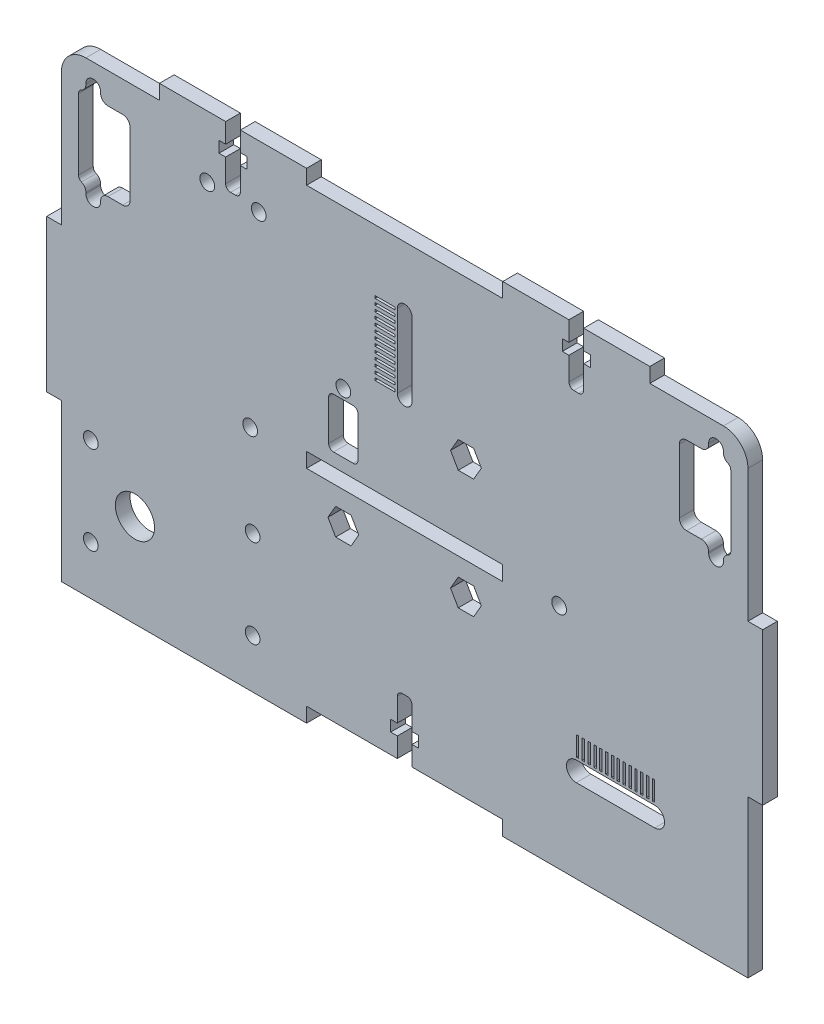
SolidWorks part; units mm, degrees
other "Marcação1"
sketch "Esboço7" plane through (-68, 31.5, 3) normal (-0.6758, 0.2828, 0.6807) x (0.7271, 0.1043, 0.6785)
sketch "Esboço8" plane through (-68, 31.5, 3) normal (-0.6758, 0.2828, 0.6807) x (0.7271, 0.1043, 0.6785)
sketch "Esboço9" plane through (-68, 31.5, 3) normal (-0.6758, 0.2828, 0.6807) x (0.7271, 0.1043, 0.6785)
sketch "Esboço10" plane through (-68, 31.5, 3) normal (-0.6758, 0.2828, 0.6807) x (0.7271, 0.1043, 0.6785)
sketch "Esboço11" plane through (-68, 36.25, 3) normal (-0.6758, 0.2828, 0.6807) x (0.7271, 0.1043, 0.6785)
sketch "Esboço13" plane through (-68, 36.25, 3) normal (-0.6758, 0.2828, 0.6807) x (0.7271, 0.1043, 0.6785)
sketch "Esboço15" plane through (-68, 36.25, 3) normal (-0.6758, 0.2828, 0.6807) x (0.7271, 0.1043, 0.6785)
sketch "Esboço19" plane through (-68, 66.25, 3) normal (-0.6758, 0.2828, 0.6807) x (0.7271, 0.1043, 0.6785)
sketch "Esboço22" plane through (-68, 95.5577, 3) normal (-0.6758, 0.2828, 0.6807) x (0.7271, 0.1043, 0.6785)
material "Acrylic (Medium-high impact)"
ref_plane "Plano frontal" through (0, 0, 0) normal (0, 0, 1) x (1, 0, 0)
ref_plane "Plano superior" through (0, 0, 0) normal (0, 1, 0) x (1, 0, 0)
ref_plane "Plano direito" through (0, 0, 0) normal (1, 0, 0) x (0, 0, -1)
sketch "Esboço1" plane through (0, 0, 0) normal (0, 0, 1) x (1, 0, 0)
  line L6 (70, -47.5) -> (-70, -47.5)
  line L8 (70, -47.5) -> (70, 47.5)
  line L9 (70, 47.5) -> (-70, 47.5)
  line L10 (-70, -47.5) -> (-70, 47.5)
  line L11 (70, -47.5) -> (-70, 47.5) construction
  line L12 (70, 47.5) -> (-70, -47.5) construction
  point P0 (0, 0)
  dimension "D1" = 95
  dimension "D2" = 140
extrude "Ressalto-extrusão1" add sketch "Esboço1" along normal mid plane 3
sketch "Esboço2" plane through (0, 0, 1.5) normal (0, 0, 1) x (1, 0, 0)
  line L1 (-20, -47.5) -> (20, -47.5)
  line L2 (-20, -47.5) -> (-20, -44.5)
  line L3 (-20, -44.5) -> (20, -44.5)
  line L4 (20, -47.5) -> (20, -44.5)
  line L6 (-70, -47.5) -> (70, -47.5) construction
  line L21 (-20, 0.5) -> (20, 0.5)
  line L22 (-20, 0.5) -> (-20, -2.5)
  line L23 (-20, -2.5) -> (20, -2.5)
  line L24 (20, 0.5) -> (20, -2.5)
  line L25 (-20, 0.5) -> (20, -2.5) construction
  line L26 (-20, -2.5) -> (20, 0.5) construction
  line L28 (0, -1.65) -> (0, 1.65) construction
  circle A2 centre (-31.5, -1) radius 1.5
  circle A4 centre (31.5, -1) radius 1.5
  point P6 (0, -44.5)
  point P14 (0, -1)
  point P29 (-20, -1)
  dimension "D4" = 11.5
  dimension "D8" = 3
  dimension "D3" = 3
  dimension "D2" = 40
  dimension "D5" = 45
  dimension "D6" = 3
  dimension "D13" = 40
extrude "Corte-extrusão1" cut sketch "Esboço2" against normal through all
sketch "Sketch9" plane through (0, 0, 0) normal (0, 0, 1) x (1, 0, 0)
  line L0 (20, -44.5) -> (-20, -44.5) construction
  line L1 (-1.5, -44.5) -> (1.5, -44.5)
  line L2 (-1.5, -44.5) -> (-1.5, -40.5)
  line L3 (-0.5, -32.5) -> (0.5, -32.5)
  line L4 (1.5, -44.5) -> (1.5, -40.5)
  line L5 (1.5, -38.23) -> (2.85, -38.23)
  line L6 (-2.85, -38.23) -> (-1.5, -38.23)
  line L7 (-2.85, -38.23) -> (-2.85, -40.5)
  line L8 (-2.85, -40.5) -> (-1.5, -40.5)
  line L9 (2.85, -38.23) -> (2.85, -40.5)
  line L10 (-1.5, -38.23) -> (-1.5, -33.5)
  line L11 (1.5, -40.5) -> (2.85, -40.5)
  line L12 (1.5, -38.23) -> (1.5, -33.5)
  arc A0 (0.5, -32.5) -> (1.5, -33.5) centre (0.5, -33.5) cw
  arc A1 (-1.5, -33.5) -> (-0.5, -32.5) centre (-0.5, -33.5) cw
  point P6 (0, -32.5)
  point P18 (1.5, -32.5)
  point P21 (-1.5, -32.5)
  dimension "D7" = 1
  dimension "D1" = 3
  dimension "D2" = 12
  dimension "D3" = 2.27
  dimension "D4" = 1.35
  dimension "D5" = 1.35
  dimension "D6" = 4
extrude "Cut-Extrude12" cut sketch "Sketch9" against normal through all both and the other way through all
sketch "Esboço3" plane through (0, 0, 1.5) normal (0, 0, 1) x (1, 0, 0)
  line L0 (70, -47.5) -> (70, 47.5) construction
  line L1 (70, 15.5) -> (73, 15.5)
  line L2 (70, 15.5) -> (70, -15.5)
  line L3 (70, -15.5) -> (73, -15.5)
  line L4 (73, 15.5) -> (73, -15.5)
  line L5 (0, -1.65) -> (0, 1.65) construction
  line L6 (-70, -15.5) -> (-73, -15.5)
  line L7 (-70, 15.5) -> (-73, 15.5)
  line L8 (-70, 15.5) -> (-70, -15.5)
  line L9 (-73, 15.5) -> (-73, -15.5)
  line L15 (70, 47.5) -> (-70, 47.5) construction
  line L16 (-50, 47.5) -> (-20, 47.5)
  line L17 (-50, 47.5) -> (-50, 50.5)
  line L18 (-50, 50.5) -> (-20, 50.5)
  line L19 (-20, 47.5) -> (-20, 50.5)
  line L20 (20, 47.5) -> (20, 50.5)
  line L21 (50, 50.5) -> (20, 50.5)
  line L22 (50, 47.5) -> (50, 50.5)
  line L23 (50, 47.5) -> (20, 47.5)
  line L24 (-70, 47.5) -> (-70, -47.5) construction
  point P6 (70, 0)
  dimension "D1" = 3
  dimension "D2" = 31
  dimension "D3" = 30
  dimension "D4" = 20
  dimension "D5" = 20
extrude "Ressalto-extrusão2" add sketch "Esboço3" against normal through all
sketch "Esboço30" plane through (0, 0, -1.5) normal (0, 0, -1) x (-1, 0, 0)
  line L0 (73, 15.5) -> (73, -15.5) construction
  line L6 (70, -47.5) -> (20, -47.5) construction
  circle A1 centre (55, -28.5) radius 4
  dimension "D1" = 18
  dimension "D2" = 19
  dimension "D3" = 8
extrude "Corte-extrusão11" cut sketch "Esboço30" against normal through all both and the other way through all
sketch "Esboço4" plane through (0, 0, 1.5) normal (0, 0, 1) x (1, 0, 0)
  line L0 (35, -28.5) -> (51, -28.5) construction
  line L1 (35, -26.5) -> (51, -26.5)
  line L2 (35, -30.5) -> (51, -30.5)
  line L4 (35, -26) -> (35.5, -26)
  line L5 (35, -26) -> (35, -22)
  line L6 (35, -22) -> (35.5, -22)
  line L7 (35.5, -26) -> (35.5, -22)
  line L8 (36.1923, -26) -> (36.6923, -26)
  line L9 (36.1923, -26) -> (36.1923, -22)
  line L10 (36.1923, -22) -> (36.6923, -22)
  line L11 (36.6923, -26) -> (36.6923, -22)
  line L12 (37.3846, -26) -> (37.8846, -26)
  line L13 (37.3846, -26) -> (37.3846, -22)
  line L14 (37.3846, -22) -> (37.8846, -22)
  line L15 (37.8846, -26) -> (37.8846, -22)
  line L16 (38.5769, -26) -> (39.0769, -26)
  line L17 (38.5769, -26) -> (38.5769, -22)
  line L18 (38.5769, -22) -> (39.0769, -22)
  line L19 (39.0769, -26) -> (39.0769, -22)
  line L20 (39.7692, -26) -> (40.2692, -26)
  line L21 (39.7692, -26) -> (39.7692, -22)
  line L22 (39.7692, -22) -> (40.2692, -22)
  line L23 (40.2692, -26) -> (40.2692, -22)
  line L24 (40.9615, -26) -> (41.4615, -26)
  line L25 (40.9615, -26) -> (40.9615, -22)
  line L26 (40.9615, -22) -> (41.4615, -22)
  line L27 (41.4615, -26) -> (41.4615, -22)
  line L28 (42.1538, -26) -> (42.6538, -26)
  line L29 (42.1538, -26) -> (42.1538, -22)
  line L30 (42.1538, -22) -> (42.6538, -22)
  line L31 (42.6538, -26) -> (42.6538, -22)
  line L32 (43.3462, -26) -> (43.8462, -26)
  line L33 (43.3462, -26) -> (43.3462, -22)
  line L34 (43.3462, -22) -> (43.8462, -22)
  line L35 (43.8462, -26) -> (43.8462, -22)
  line L36 (44.5385, -26) -> (45.0385, -26)
  line L37 (44.5385, -26) -> (44.5385, -22)
  line L38 (44.5385, -22) -> (45.0385, -22)
  line L39 (45.0385, -26) -> (45.0385, -22)
  line L40 (45.7308, -26) -> (46.2308, -26)
  line L41 (45.7308, -26) -> (45.7308, -22)
  line L42 (45.7308, -22) -> (46.2308, -22)
  line L43 (46.2308, -26) -> (46.2308, -22)
  line L44 (46.9231, -26) -> (47.4231, -26)
  line L45 (46.9231, -26) -> (46.9231, -22)
  line L46 (46.9231, -22) -> (47.4231, -22)
  line L47 (47.4231, -26) -> (47.4231, -22)
  line L48 (48.1154, -26) -> (48.6154, -26)
  line L49 (48.1154, -26) -> (48.1154, -22)
  line L50 (48.1154, -22) -> (48.6154, -22)
  line L51 (48.6154, -26) -> (48.6154, -22)
  line L52 (49.3077, -26) -> (49.8077, -26)
  line L53 (49.3077, -26) -> (49.3077, -22)
  line L54 (49.3077, -22) -> (49.8077, -22)
  line L55 (49.8077, -26) -> (49.8077, -22)
  line L56 (50.5, -26) -> (51, -26)
  line L57 (50.5, -26) -> (50.5, -22)
  line L58 (50.5, -22) -> (51, -22)
  line L59 (51, -26) -> (51, -22)
  line L60 (20, -47.5) -> (70, -47.5) construction
  arc A9 (35, -26.5) -> (35, -30.5) centre (35, -28.5) ccw
  circle A10 centre (43, -28.5) radius 2 construction
  arc A12 (51, -30.5) -> (51, -26.5) centre (51, -28.5) ccw
  circle A13 centre (-55, -28.5) radius 4 construction
  point P8 (43, -28.5)
  dimension "D1" = 98
  dimension "D4" = 0.5
  dimension "D3" = 8
  dimension "D2" = 4
  dimension "D5" = 4
  dimension "D6" = 14
  dimension "D7" = 0.5
  dimension "D8" = 19
extrude "Corte-extrusão2" cut sketch "Esboço4" against normal through all
sketch "Esboço31" plane through (0, 0, -1.5) normal (0, 0, -1) x (-1, 0, 0)
  line L0 (73, -15.5) -> (70, -15.5) construction
  line L1 (70, -15.5) -> (70, -47.5) construction
  circle A4 centre (64, -19.5) radius 1.5
  circle A5 centre (64, -37.5) radius 1.5
  circle A7 centre (31, -19.5) radius 1.5
  circle A8 centre (31, -37.5) radius 1.5
  dimension "D1" = 3
  dimension "D2" = 4
  dimension "D3" = 6
  dimension "D4" = 18
  dimension "D5" = 33
extrude "Corte-extrusão12" cut sketch "Esboço31" against normal through all both and the other way through all
sketch "Sketch8" plane through (0, 0, -1.5) normal (0, 0, -1) x (-1, 0, 0)
  line L2 (-70, 47.5) -> (-50, 47.5) construction
  line L4 (0, 1.65) -> (0, -1.65) construction
  line L5 (-70, 15.5) -> (-70, 47.5) construction
  line B0 (-70, 33.25) -> (-56, 33.25) construction
  line B1 (-70, 39.75) -> (-70, 26.75) construction
  line B2 (-56, 39.75) -> (-56, 26.75)
  line B3 (-65, 23.5) -> (-65, 23.75)
  line B4 (-62, 23.5) -> (-62, 23.75)
  line B5 (-60.5, 25.25) -> (-57.5, 25.25)
  line B6 (-65, 43) -> (-65, 42.75)
  line B7 (-62, 43) -> (-62, 42.75)
  line B8 (-60.5, 41.25) -> (-57.5, 41.25)
  line B9 (-66.5, 40.4587) -> (-66.5, 26.0413)
  arc B10 (-62, 43) -> (-65, 43) centre (-63.5, 43) ccw
  arc B11 (-65, 23.5) -> (-62, 23.5) centre (-63.5, 23.5) ccw
  arc B12 (-62, 23.75) -> (-60.5, 25.25) centre (-60.5, 23.75) cw
  arc B13 (-65, 23.75) -> (-65.9, 25.1248) centre (-66.5, 23.75) ccw
  arc B14 (-62, 42.75) -> (-60.5, 41.25) centre (-60.5, 42.75) ccw
  arc B15 (-65, 42.75) -> (-65.9, 41.3752) centre (-66.5, 42.75) cw
  arc B16 (-57.5, 25.25) -> (-56, 26.75) centre (-57.5, 26.75) ccw
  arc B17 (-57.5, 41.25) -> (-56, 39.75) centre (-57.5, 39.75) cw
  arc B18 (-66.5, 26.0413) -> (-65.9, 25.1248) centre (-65.5, 26.0413) ccw
  arc B19 (-66.5, 40.4587) -> (-65.9, 41.3752) centre (-65.5, 40.4587) cw
  line B20 (70, 33.25) -> (56, 33.25) construction
  line B21 (56, 39.75) -> (56, 26.75)
  line B22 (65, 23.5) -> (65, 23.75)
  line B23 (62, 23.5) -> (62, 23.75)
  line B24 (60.5, 25.25) -> (57.5, 25.25)
  line B25 (65, 43) -> (65, 42.75)
  line B26 (62, 43) -> (62, 42.75)
  line B27 (60.5, 41.25) -> (57.5, 41.25)
  line B28 (66.5, 40.4587) -> (66.5, 26.0413)
  arc B29 (62, 43) -> (65, 43) centre (63.5, 43) cw
  arc B30 (65, 23.5) -> (62, 23.5) centre (63.5, 23.5) cw
  arc B31 (62, 23.75) -> (60.5, 25.25) centre (60.5, 23.75) ccw
  arc B32 (65, 23.75) -> (65.9, 25.1248) centre (66.5, 23.75) cw
  arc B33 (62, 42.75) -> (60.5, 41.25) centre (60.5, 42.75) cw
  arc B34 (65, 42.75) -> (65.9, 41.3752) centre (66.5, 42.75) ccw
  arc B35 (57.5, 25.25) -> (56, 26.75) centre (57.5, 26.75) cw
  arc B36 (57.5, 41.25) -> (56, 39.75) centre (57.5, 39.75) ccw
  arc B37 (66.5, 26.0413) -> (65.9, 25.1248) centre (65.5, 26.0413) cw
  arc B38 (66.5, 40.4587) -> (65.9, 41.3752) centre (65.5, 40.4587) ccw
  dimension "D3" = 3
sketch_block_instance "Block6-1"
sketch_block "Block6" parameters "D1"=3, "D2"=1.5, "D3"=1.5, "D5"=1, "D4"=5, "D6"=6.5
sketch_block_instance "Block6-4"
extrude "Cut-Extrude11" cut sketch "Sketch8" against normal through all both and the other way through all
sketch "Sketch11" plane through (0, 0, 0) normal (0, 0, 1) x (1, 0, 0)
  line L0 (50, 50.5) -> (20, 50.5) construction
  line L1 (33.5, 50.5) -> (36.5, 50.5)
  line L2 (33.5, 50.5) -> (33.5, 46.5)
  line L3 (34.5, 38.5) -> (35.5, 38.5)
  line L4 (36.5, 50.5) -> (36.5, 46.5)
  line L5 (20, 50.5) -> (20, 47.5) construction
  line L6 (33.5, 44.23) -> (33.5, 39.5)
  line L7 (32.15, 46.5) -> (33.5, 46.5)
  line L8 (32.15, 46.5) -> (32.15, 44.23)
  line L9 (32.15, 44.23) -> (33.5, 44.23)
  line L10 (37.85, 46.5) -> (37.85, 44.23)
  line L11 (36.5, 46.5) -> (37.85, 46.5)
  line L12 (36.5, 44.23) -> (36.5, 39.5)
  line L13 (36.5, 44.23) -> (37.85, 44.23)
  line L14 (0, -1.65) -> (0, 1.65) construction
  line L15 (-36.5, 44.23) -> (-37.85, 44.23)
  line L16 (-36.5, 44.23) -> (-36.5, 39.5)
  line L17 (-36.5, 46.5) -> (-37.85, 46.5)
  line L18 (-37.85, 46.5) -> (-37.85, 44.23)
  line L19 (-32.15, 44.23) -> (-33.5, 44.23)
  line L20 (-32.15, 46.5) -> (-32.15, 44.23)
  line L21 (-32.15, 46.5) -> (-33.5, 46.5)
  line L22 (-33.5, 44.23) -> (-33.5, 39.5)
  line L23 (-36.5, 50.5) -> (-36.5, 46.5)
  line L24 (-34.5, 38.5) -> (-35.5, 38.5)
  line L25 (-33.5, 50.5) -> (-33.5, 46.5)
  line L26 (-33.5, 50.5) -> (-36.5, 50.5)
  arc A0 (35.5, 38.5) -> (36.5, 39.5) centre (35.5, 39.5) ccw
  arc A1 (33.5, 39.5) -> (34.5, 38.5) centre (34.5, 39.5) ccw
  arc A2 (-33.5, 39.5) -> (-34.5, 38.5) centre (-34.5, 39.5) cw
  arc A3 (-35.5, 38.5) -> (-36.5, 39.5) centre (-35.5, 39.5) cw
  point P20 (33.5, 38.5)
  point P39 (-33.5, 38.5)
  dimension "D8" = 1
  dimension "D1" = 3
  dimension "D2" = 12
  dimension "D3" = 13.5
  dimension "D4" = 1.35
  dimension "D5" = 2.27
  dimension "D6" = 1.35
  dimension "D7" = 4
extrude "Cut-Extrude14" cut sketch "Sketch11" against normal through all both and the other way through all
sketch "Sketch12" plane through (0, 0, 1.5) normal (0, 0, 1) x (1, 0, 0)
  line L0 (0, 0.5) -> (0, 47.5) construction
  line L1 (20, 0.5) -> (-20, 0.5) construction
  line L2 (20, 47.5) -> (-20, 47.5) construction
  line L3 (0, 20) -> (0, 35) construction
  line L6 (-1.5, 20) -> (-1.5, 35)
  line L7 (1.5, 20) -> (1.5, 35)
  line L8 (-2, 21.2083) -> (-6, 21.2083)
  line L9 (-2, 20) -> (-6, 20)
  line L10 (-2, 20) -> (-2, 20.5)
  line L11 (-2, 20.5) -> (-6, 20.5)
  line L12 (-6, 20) -> (-6, 20.5)
  line L13 (-2, 21.2083) -> (-2, 21.7083)
  line L14 (-2, 21.7083) -> (-6, 21.7083)
  line L15 (-6, 21.2083) -> (-6, 21.7083)
  line L16 (-2, 22.4167) -> (-6, 22.4167)
  line L17 (-2, 22.4167) -> (-2, 22.9167)
  line L18 (-2, 22.9167) -> (-6, 22.9167)
  line L19 (-6, 22.4167) -> (-6, 22.9167)
  line L20 (-2, 23.625) -> (-6, 23.625)
  line L21 (-2, 23.625) -> (-2, 24.125)
  line L22 (-2, 24.125) -> (-6, 24.125)
  line L23 (-6, 23.625) -> (-6, 24.125)
  line L24 (-2, 24.8333) -> (-6, 24.8333)
  line L25 (-2, 24.8333) -> (-2, 25.3333)
  line L26 (-2, 25.3333) -> (-6, 25.3333)
  line L27 (-6, 24.8333) -> (-6, 25.3333)
  line L28 (-2, 26.0417) -> (-6, 26.0417)
  line L29 (-2, 26.0417) -> (-2, 26.5417)
  line L30 (-2, 26.5417) -> (-6, 26.5417)
  line L31 (-6, 26.0417) -> (-6, 26.5417)
  line L32 (-2, 27.25) -> (-6, 27.25)
  line L33 (-2, 27.25) -> (-2, 27.75)
  line L34 (-2, 27.75) -> (-6, 27.75)
  line L35 (-6, 27.25) -> (-6, 27.75)
  line L36 (-2, 28.4583) -> (-6, 28.4583)
  line L37 (-2, 28.4583) -> (-2, 28.9583)
  line L38 (-2, 28.9583) -> (-6, 28.9583)
  line L39 (-6, 28.4583) -> (-6, 28.9583)
  line L40 (-2, 29.6667) -> (-6, 29.6667)
  line L41 (-2, 29.6667) -> (-2, 30.1667)
  line L42 (-2, 30.1667) -> (-6, 30.1667)
  line L43 (-6, 29.6667) -> (-6, 30.1667)
  line L44 (-2, 30.875) -> (-6, 30.875)
  line L45 (-2, 30.875) -> (-2, 31.375)
  line L46 (-2, 31.375) -> (-6, 31.375)
  line L47 (-6, 30.875) -> (-6, 31.375)
  line L48 (-2, 32.0833) -> (-6, 32.0833)
  line L49 (-2, 32.0833) -> (-2, 32.5833)
  line L50 (-2, 32.5833) -> (-6, 32.5833)
  line L51 (-6, 32.0833) -> (-6, 32.5833)
  line L52 (-2, 33.2917) -> (-6, 33.2917)
  line L53 (-2, 33.2917) -> (-2, 33.7917)
  line L54 (-2, 33.7917) -> (-6, 33.7917)
  line L55 (-6, 33.2917) -> (-6, 33.7917)
  line L56 (-2, 34.5) -> (-6, 34.5)
  line L57 (-2, 34.5) -> (-2, 35)
  line L58 (-2, 35) -> (-6, 35)
  line L59 (-6, 34.5) -> (-6, 35)
  circle A1 centre (0, 20) radius 1.5 construction
  arc A4 (-1.5, 20) -> (1.5, 20) centre (0, 20) ccw
  arc A5 (1.5, 35) -> (-1.5, 35) centre (0, 35) ccw
  point P4 (0, 27.5)
  dimension "D1" = 3
  dimension "D2" = 15
  dimension "D3" = 0.5
  dimension "D4" = 18
  dimension "D5" = 4
  dimension "D6" = 0.5
  dimension "D7" = 13
extrude "Cut-Extrude15" cut sketch "Sketch12" against normal through all
sketch "Sketch13" plane through (0, 0, 0) normal (0, 0, 1) x (1, 0, 0)
  line L15 (20, 0.5) -> (-20, 0.5) construction
  line L16 (20, -2.5) -> (20, 0.5) construction
  line L18 (-10.5, 13.35) -> (-14.5, 13.35)
  line L19 (-9.5, 12.35) -> (-9.5, 4.15)
  line L20 (-10.5, 3.15) -> (-14.5, 3.15)
  line L21 (-15.5, 12.35) -> (-15.5, 4.15)
  line L23 (15.64, 15.35) -> (14.07, 18.0693)
  line L24 (14.07, 18.0693) -> (10.93, 18.0693)
  line L25 (10.93, 18.0693) -> (9.36, 15.35)
  line L26 (9.36, 15.35) -> (10.93, 12.6307)
  line L27 (10.93, 12.6307) -> (14.07, 12.6307)
  line L28 (14.07, 12.6307) -> (15.64, 15.35)
  line L30 (15.64, -8.95) -> (14.07, -6.2307)
  line L31 (14.07, -6.2307) -> (10.93, -6.2307)
  line L32 (10.93, -6.2307) -> (9.36, -8.95)
  line L33 (9.36, -8.95) -> (10.93, -11.6693)
  line L34 (10.93, -11.6693) -> (14.07, -11.6693)
  line L35 (14.07, -11.6693) -> (15.64, -8.95)
  line L36 (-20, -2.5) -> (20, -2.5) construction
  line L38 (-9.36, -8.95) -> (-10.93, -6.2307)
  line L39 (-10.93, -6.2307) -> (-14.07, -6.2307)
  line L40 (-14.07, -6.2307) -> (-15.64, -8.95)
  line L41 (-15.64, -8.95) -> (-14.07, -11.6693)
  line L42 (-14.07, -11.6693) -> (-10.93, -11.6693)
  line L43 (-10.93, -11.6693) -> (-9.36, -8.95)
  circle A1 centre (12.5, 15.35) radius 1.5 construction
  circle A2 centre (-12.5, -8.95) radius 1.5 construction
  circle A3 centre (12.5, -8.95) radius 1.5 construction
  circle A10 centre (-12.5, 15.35) radius 1.5
  arc A11 (-14.5, 3.15) -> (-15.5, 4.15) centre (-14.5, 4.15) cw
  arc A12 (-9.5, 4.15) -> (-10.5, 3.15) centre (-10.5, 4.15) cw
  arc A13 (-14.5, 13.35) -> (-15.5, 12.35) centre (-14.5, 12.35) ccw
  arc A14 (-10.5, 13.35) -> (-9.5, 12.35) centre (-10.5, 12.35) cw
  circle A15 centre (12.5, 15.35) radius 2.7193 construction
  circle A16 centre (12.5, -8.95) radius 2.7193 construction
  circle A17 centre (-12.5, -8.95) radius 2.7193 construction
  point P16 (-12.5, 13.35)
  point P19 (-15.5, 3.15)
  point P25 (-15.5, 13.35)
  dimension "D5" = 7.5
  dimension "D1" = 3
  dimension "D3" = 25
  dimension "D2" = 24.3
  dimension "D6" = 0.5
  dimension "D4" = 13.35
  dimension "D9" = 1
  dimension "D10" = 3.14
  dimension "D7" = 10.2
  dimension "D8" = 1.5
extrude "Cut-Extrude16" cut sketch "Sketch13" against normal through all both and the other way through all
fillet "Fillet1" radius 5 2 edges at (70, 47.5, 0) (-70, 47.5, 0)
sketch "Sketch14" plane through (0, 0, 0) normal (0, 0, 1) x (1, 0, 0)
  line L0 (-35, 42.1706) -> (-35, 58.8294) construction
  line L1 (-50, 50.5) -> (-20, 50.5) construction
  line L3 (20, 47.5) -> (-20, 47.5) construction
  circle A0 centre (-29.75, 37.9) radius 1.5
  circle A1 centre (-40.25, 37.9) radius 1.5
  point P5 (-35, 50.5)
  point P7 (-35, 50.5)
  dimension "D1" = 3
  dimension "D2" = 10.5
  dimension "D3" = 9.6
extrude "Cut-Extrude17" cut sketch "Sketch14" against normal through all both and the other way through all
